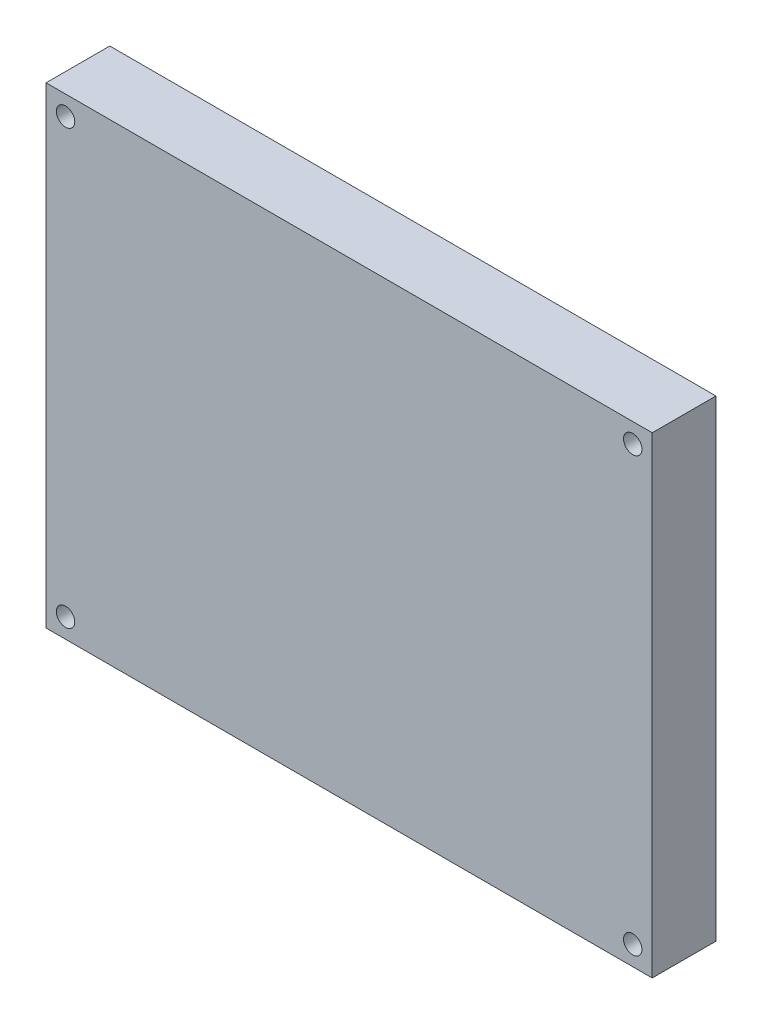
SolidWorks part; units mm, degrees
ref_plane "Спереди" through (0, 0, 0) normal (0, 0, 1) x (1, 0, 0)
ref_plane "Сверху" through (0, 0, 0) normal (0, 1, 0) x (1, 0, 0)
ref_plane "Справа" through (0, 0, 0) normal (1, 0, 0) x (0, 0, -1)
sketch "Эскиз1" plane through (0, 0, 0) normal (0, 0, 1) x (1, 0, 0)
  line L1 (-92.5455, 61.4567) -> (2.6045, 61.4567)
  line L2 (-92.5455, 61.4567) -> (-92.5455, -12.6633)
  line L3 (-92.5455, -12.6633) -> (2.6045, -12.6633)
  line L4 (2.6045, 61.4567) -> (2.6045, -12.6633)
  line L5 (-92.5455, 61.4567) -> (2.6045, -12.6633) construction
  line L6 (-92.5455, -12.6633) -> (2.6045, 61.4567) construction
  circle A2 centre (-0.4555, 58.3967) radius 1.445
  circle A3 centre (-89.4855, 58.3967) radius 1.445
  circle A4 centre (-89.4855, -9.6033) radius 1.445
  circle A5 centre (-0.4555, -9.6033) radius 1.445
  point P0 (-44.9705, 24.3967)
  dimension "D3" = 3.06
  dimension "D4" = 3.06
  dimension "D5" = 3.06
  dimension "D7" = 3.06
  dimension "D9" = 3.06
  dimension "D1" = 95.15
  dimension "D2" = 74.12
  dimension "D6" = 3.06
  dimension "D8" = 3.06
  dimension "D10" = 3.06
extrude "Бобышка-Вытянуть1" add sketch "Эскиз1" along normal blind 10
